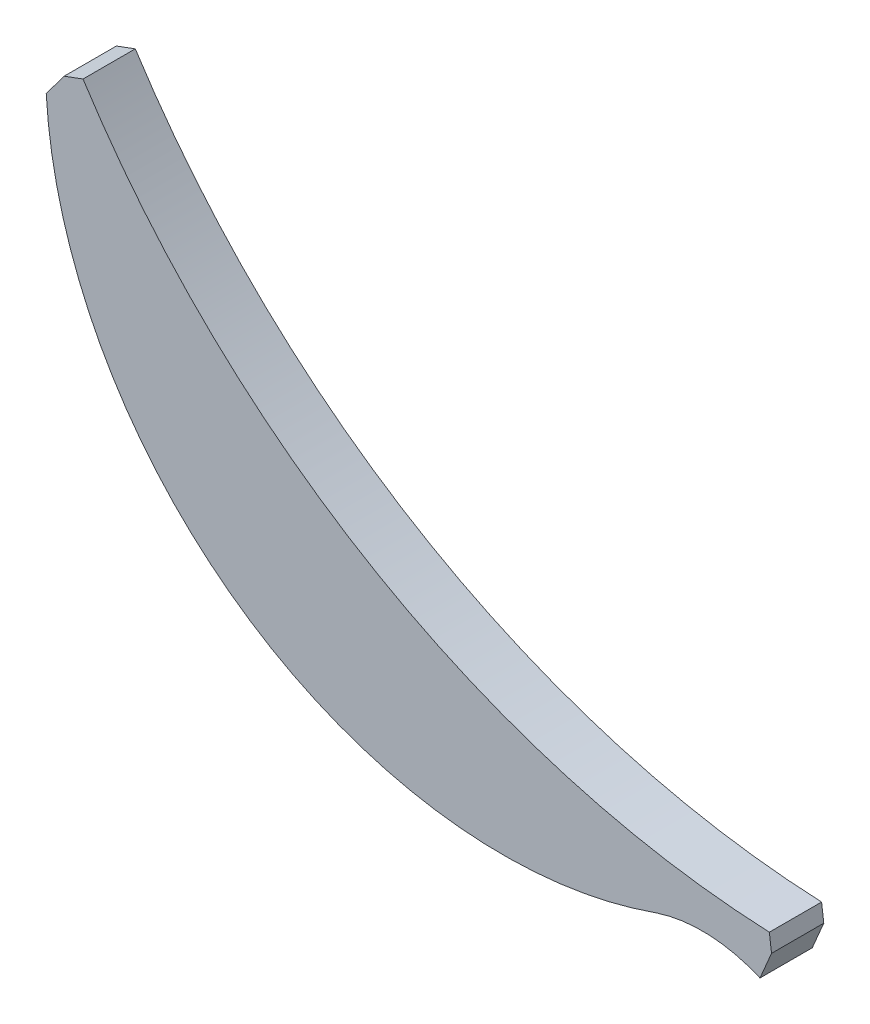
SolidWorks part; units mm, degrees
ref_plane "Alzado" through (0, 0, 0) normal (0, 0, 1) x (1, 0, 0)
ref_plane "Planta" through (0, 0, 0) normal (0, 1, 0) x (1, 0, 0)
ref_plane "Vista lateral" through (0, 0, 0) normal (1, 0, 0) x (0, 0, -1)
sketch "Model" plane through (0, 0, 0) normal (0, 0, 1) x (1, 0, 0)
  line L0 (49.556, 5.6971) -> (50.2179, 7.2533)
  line L1 (50.2179, 7.2533) -> (50.0925, 8.2432)
  line L3 (8.5821, 29.1795) -> (9.611, 30.5573)
  line L4 (9.611, 30.5573) -> (10.6948, 30.9584)
  arc A0 (11.0755, 19.4463) -> (43.61, 5.9602) centre (34.8076, 30.7119) ccw
  arc A1 (49.556, 5.6971) -> (43.61, 5.9602) centre (46.2369, -1.994) ccw
  arc A2 (8.5821, 29.1795) -> (11.0755, 19.4463) centre (34.8076, 30.7119) ccw
  arc A3 (10.6948, 30.9584) -> (50.0925, 8.2432) centre (52.2749, 57.5521) ccw
extrude "Saliente-Extruir1" add sketch "Model" along normal blind 3
